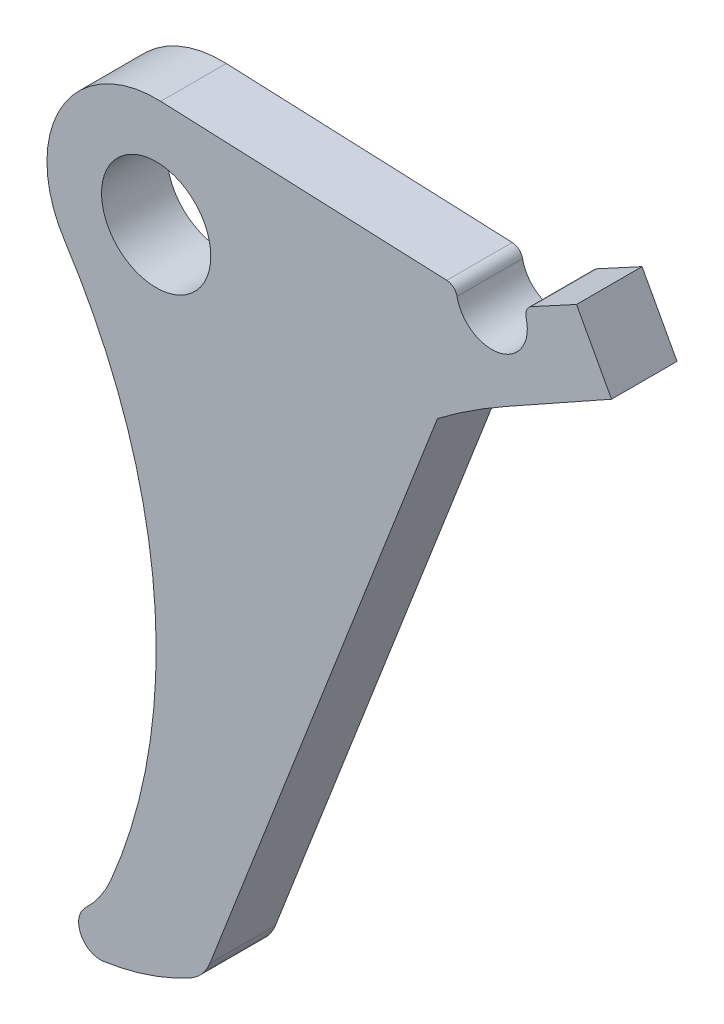
SolidWorks part; units mm, degrees
material "AISI 1020"
ref_plane "Спереди" through (0, 0, 0) normal (0, 0, 1) x (1, 0, 0)
ref_plane "Сверху" through (0, 0, 0) normal (0, 1, 0) x (1, 0, 0)
ref_plane "Справа" through (0, 0, 0) normal (1, 0, 0) x (0, 0, -1)
sketch "Эскиз1" plane through (0, 0, 0) normal (0, 0, 1) x (1, 0, 0)
  line L0 (4.9162, -56.1204) -> (25.76, -2.4865) construction
  line L1 (31.992, 1.5794) -> (41.6932, 7.0057) construction
  line L2 (41.6932, 7.0057) -> (38.4899, 12.9203) construction
  line L3 (38.4899, 12.9203) -> (34.3652, 10.6864) construction
  line L4 (0.4192, 9.9912) -> (26.606, 8.8924) construction
  line L5 (4.9162, -56.1204) -> (25.76, -2.4865)
  line L6 (31.992, 1.5794) -> (41.6932, 7.0057)
  line L7 (41.6932, 7.0057) -> (38.4899, 12.9203)
  line L8 (38.4899, 12.9203) -> (34.3652, 10.6864)
  line L9 (0.4192, 9.9912) -> (26.606, 8.8924)
  circle A0 centre (0, 0) radius 5 construction
  arc A1 (-6.4763, -57.3991) -> (-4.1601, -54.0681) centre (-13.3577, -50.1434) ccw construction
  arc A2 (-6.4763, -57.3991) -> (-4.8061, -60.8285) centre (-5.1, -58.8502) ccw construction
  arc A3 (-4.8061, -60.8285) -> (3.098, -58.186) centre (-8.3192, -37.1786) ccw construction
  arc A4 (3.098, -58.186) -> (4.9162, -56.1204) centre (1.1879, -54.6715) ccw construction
  arc A5 (31.992, 1.5794) -> (25.76, -2.4865) centre (58.6904, -46.1515) ccw construction
  arc A6 (34.3652, 10.6864) -> (33.8748, 9.5511) centre (34.8415, 9.8071) ccw construction
  arc A7 (27.545, 8.0876) -> (33.8748, 9.5511) centre (30.7331, 8.7192) ccw construction
  arc A8 (27.545, 8.0876) -> (26.606, 8.8924) centre (26.5641, 7.8933) ccw construction
  arc A9 (0.4192, 9.9912) -> (-8.3831, -5.4519) centre (0, 0) ccw construction
  arc A10 (-4.1601, -54.0681) -> (-8.3831, -5.4519) centre (-51.8486, -33.719) ccw construction
  circle A11 centre (0, 0) radius 5
  arc A12 (-6.4763, -57.3991) -> (-4.1601, -54.0681) centre (-13.3577, -50.1434) ccw
  arc A13 (-6.4763, -57.3991) -> (-4.8061, -60.8285) centre (-5.1, -58.8502) ccw
  arc A14 (-4.8061, -60.8285) -> (3.098, -58.186) centre (-8.3192, -37.1786) ccw
  arc A15 (3.098, -58.186) -> (4.9162, -56.1204) centre (1.1879, -54.6715) ccw
  arc A16 (31.992, 1.5794) -> (25.76, -2.4865) centre (58.6904, -46.1515) ccw
  arc A17 (34.3652, 10.6864) -> (33.8748, 9.5511) centre (34.8415, 9.8071) ccw
  arc A18 (27.545, 8.0876) -> (33.8748, 9.5511) centre (30.7331, 8.7192) ccw
  arc A19 (27.545, 8.0876) -> (26.606, 8.8924) centre (26.5641, 7.8933) ccw
  arc A20 (0.4192, 9.9912) -> (-8.3831, -5.4519) centre (0, 0) ccw
  arc A21 (-4.1601, -54.0681) -> (-8.3831, -5.4519) centre (-51.8486, -33.719) ccw
extrude "Бобышка-Вытянуть1" add sketch "Эскиз1" along normal mid plane 6
